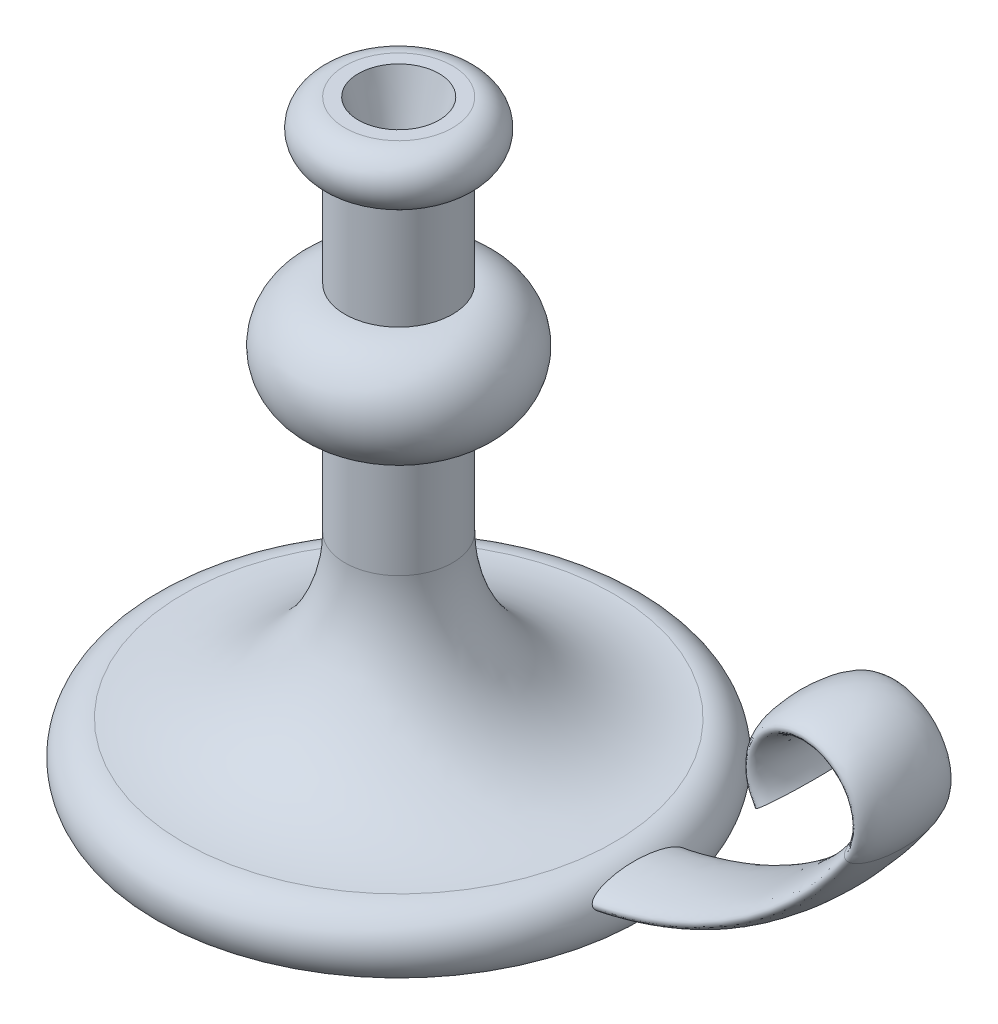
SolidWorks part; units mm, degrees
material "Glass"
ref_plane "Front Plane" through (0, 0, 0) normal (0, 0, 1) x (1, 0, 0)
ref_plane "Top Plane" through (0, 0, 0) normal (0, 1, 0) x (1, 0, 0)
ref_plane "Right Plane" through (0, 0, 0) normal (1, 0, 0) x (0, 0, -1)
sketch "Sketch1" plane through (0, 0, 0) normal (0, 0, 1) x (1, 0, 0)
  line L0 (0, 0) -> (0, 220)
  line L1 (0, 220) -> (20, 220)
  line L2 (20, 200) -> (20, 160)
  line L3 (20, 120) -> (20, 80)
  line L4 (90, 0) -> (0, 0)
  arc A0 (20, 220) -> (20, 200) centre (20, 210) cw
  arc A1 (20, 160) -> (20, 120) centre (20, 140) cw
  arc A2 (20, 80) -> (80, 20) centre (80, 80) ccw
  arc A3 (80, 20) -> (90, 0) centre (80, 7.5) cw
  dimension "D3" = 10
  dimension "D5" = 20
  dimension "D6" = 60
  dimension "D7" = 12.5
  dimension "D1" = 220
  dimension "D2" = 20
  dimension "D4" = 40
  dimension "D8" = 80
  dimension "D9" = 90
revolve "Revolve1" add sketch "Sketch1" angle 360 about L0
sketch "Sketch2" plane through (0, 0, 0) normal (0, 0, 1) x (1, 0, 0)
  line L0 (0, 10) -> (60, 10)
  line L1 (-90, 0) -> (90, 0) construction
  arc A0 (60, 10) -> (183.5921, 75) centre (60, 160) ccw
  arc A1 (183.5921, 75) -> (150.6342, 75) centre (167.1131, 86.3333) ccw
  dimension "D3" = 150
  dimension "D5" = 20
  dimension "D1" = 60
  dimension "D2" = 10
  dimension "D4" = 65
sketch "Sketch3" plane through (0, 0, 0) normal (1, 0, 0) x (0, 0, -1)
  ellipse E0 centre (0, 10) end of major axis (-17.5, 10) minor radius 5
  dimension "D1" = 35
  dimension "D2" = 10
  dimension "D3" = 10
sweep "Sweep1" add profiles "Sketch3" path "Sketch2"
sketch "Sketch4" plane through (0, 220, 0) normal (0, 1, 0) x (1, 0, 0)
  circle A0 centre (0, 0) radius 15
  dimension "D1" = 30
extrude "Cut-Extrude1" cut sketch "Sketch4" against normal blind 25 draft 15
